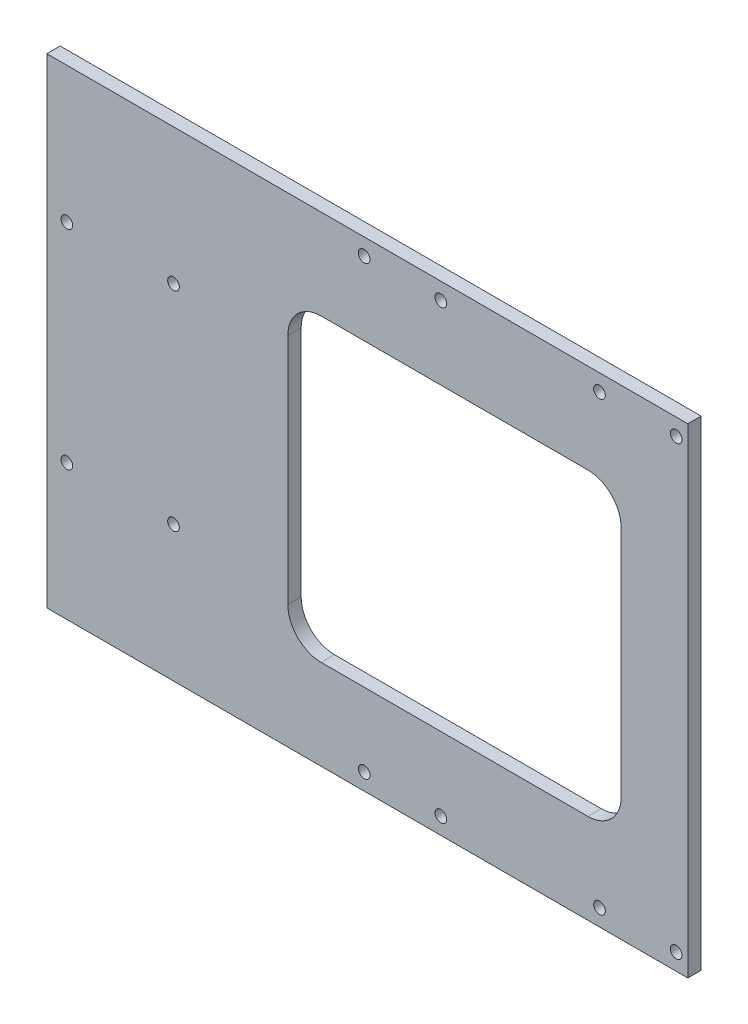
SolidWorks part; units mm, degrees
ref_plane "正面" through (0, 0, 0) normal (0, 0, 1) x (1, 0, 0)
ref_plane "平面" through (0, 0, 0) normal (0, 1, 0) x (1, 0, 0)
ref_plane "右側面" through (0, 0, 0) normal (1, 0, 0) x (0, 0, -1)
sketch "ｽｹｯﾁ1" plane through (0, 0, 0) normal (0, 0, 1) x (1, 0, 0)
  line L0 (96.15, -72) -> (96.15, 72) construction
  line L1 (96.15, -72) -> (-96.15, -72)
  line L2 (96.15, -72) -> (96.15, 72)
  line L3 (96.15, 72) -> (-96.15, 72)
  line L4 (-96.15, -72) -> (-96.15, 72)
  line L5 (96.15, -72) -> (-96.15, 72) construction
  line L6 (96.15, 72) -> (-96.15, -72) construction
  line L7 (-96.15, 0) -> (96.15, 0)
  circle A0 centre (92.65, 67) radius 1.75
  circle A1 centre (69.65, 67) radius 1.75
  circle A2 centre (22.05, 67) radius 1.75
  circle A3 centre (-0.95, 67) radius 1.75
  circle A4 centre (-0.95, -67) radius 1.75
  circle A5 centre (22.05, -67) radius 1.75
  circle A6 centre (69.65, -67) radius 1.75
  circle A7 centre (92.65, -67) radius 1.75
  circle A8 centre (-90.15, 31.25) radius 1.75
  circle A9 centre (-90.15, -31.25) radius 1.75
  circle A10 centre (-58.15, 31.25) radius 1.75
  circle A11 centre (-58.15, -31.25) radius 1.75
  point P0 (0, 0)
  point P19 (0, 0)
  dimension "D3" = 3.5
  dimension "D6" = 3.5
  dimension "D9" = 3.5
  dimension "D11" = 3.5
  dimension "D13" = 3.5
  dimension "D16" = 3.5
  dimension "D1" = 144
  dimension "D2" = 192.3
  dimension "D4" = 3.5
  dimension "D5" = 5
  dimension "D7" = 5
  dimension "D8" = 23
  dimension "D10" = 47.6
  dimension "D12" = 23
  dimension "D14" = 6
  dimension "D15" = 31.25
  dimension "D17" = 32
extrude "ﾎﾞｽ - 押し出し1" add sketch "ｽｹｯﾁ1" along normal blind 4 contours L4 L7 L2 L3 A3 A2 A1 A0 | L7 L4 L1 L2 A6 A4 A5 A7
sketch "ｽｹｯﾁ2" plane through (0, 0, 4) normal (0, 0, 1) x (1, 0, 0)
  line L0 (96.15, -72) -> (96.15, 72) construction
  line L1 (76.15, -45) -> (-23.85, -45)
  line L2 (76.15, -45) -> (76.15, 45)
  line L3 (76.15, 45) -> (-23.85, 45)
  line L4 (-23.85, -45) -> (-23.85, 45)
  line L5 (76.15, -45) -> (-23.85, 45) construction
  line L6 (76.15, 45) -> (-23.85, -45) construction
  point P0 (26.15, 0)
  dimension "D1" = 100
  dimension "D2" = 90
  dimension "D3" = 0
  dimension "D4" = 20
extrude "ｶｯﾄ - 押し出し1" cut sketch "ｽｹｯﾁ2" against normal blind 10
fillet "ﾌｨﾚｯﾄ1" radius 10 4 edges at (-23.85, -45, 2) (76.15, -45, 2) (76.15, 45, 2) (-23.85, 45, 2)
